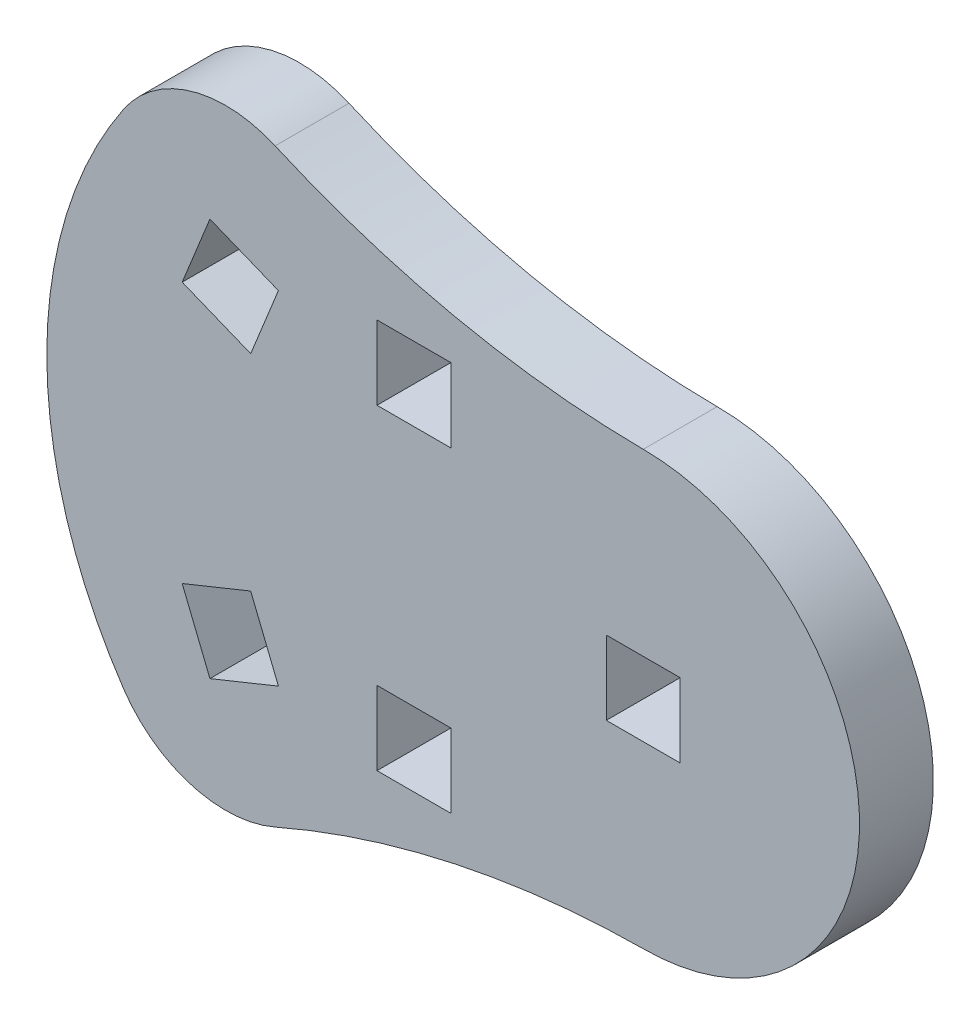
SolidWorks part; units mm, degrees
ref_plane "Front Plane" through (0, 0, 0) normal (0, 0, 1) x (1, 0, 0)
ref_plane "Top Plane" through (0, 0, 0) normal (0, 1, 0) x (1, 0, 0)
ref_plane "Right Plane" through (0, 0, 0) normal (1, 0, 0) x (0, 0, -1)
sketch "Sketch1" plane through (0, 0, 0) normal (0, 0, 1) x (1, 0, 0)
  line L0 (-6.7064, -5.985) -> (-6.7064, 4.461) construction
  line L1 (-1.524, -4.7878) -> (0, -4.7878)
  line L2 (-1.524, -4.7878) -> (-1.524, -3.2638)
  line L3 (-1.524, -3.2638) -> (0, -3.2638)
  line L4 (0, -4.7878) -> (0, -3.2638)
  line L5 (0, 1.7398) -> (-1.524, 1.7398)
  line L6 (0, 1.7398) -> (0, 3.2638)
  line L7 (0, 3.2638) -> (-1.524, 3.2638)
  line L8 (-1.524, 1.7398) -> (-1.524, 3.2638)
  line L9 (-6.7064, -5.223) -> (-6.7064, -6.747) construction
  line L10 (-6.7064, 5.223) -> (-6.7064, 3.699) construction
  line L12 (7.1074, 0) -> (0, 0) construction
  line L13 (3.9675, -1.524) -> (3.9675, 0) construction
  line L14 (-3.5039, -0.762) -> (1.0475, -0.762) construction
  line L15 (-3.5039, -1.524) -> (-3.5039, 0) construction
  line L16 (3.2055, -1.524) -> (4.7295, -1.524)
  line L17 (3.2055, -1.524) -> (3.2055, 0)
  line L18 (3.2055, 0) -> (4.7295, 0)
  line L19 (4.7295, -1.524) -> (4.7295, 0)
  line L20 (3.2055, -1.524) -> (4.7295, 0) construction
  line L21 (3.2055, 0) -> (4.7295, -1.524) construction
  line L22 (-5.5425, 1.9299) -> (-4.9707, 3.3425)
  line L23 (-4.1298, -2.882) -> (-5.5425, -3.4539)
  line L24 (-3.558, -4.2947) -> (-4.9707, -4.8665)
  line L25 (-4.1298, -2.882) -> (-3.558, -4.2947)
  line L26 (-5.5425, -3.4539) -> (-4.9707, -4.8665)
  line L27 (-4.1298, 1.358) -> (-3.558, 2.7707)
  line L28 (-3.558, 2.7707) -> (-4.9707, 3.3425)
  line L29 (-4.1298, 1.358) -> (-5.5425, 1.9299)
  arc A0 (-3.6258, -6.8461) -> (-6.7503, -5.9412) centre (-4.6453, -4.5197) cw
  arc A1 (-3.6258, 5.3221) -> (-6.7503, 4.4172) centre (-4.6453, 2.9957) ccw
  arc A2 (3.9675, -5.223) -> (3.9675, 3.699) centre (3.9675, -0.762) ccw
  arc A3 (3.9675, 3.699) -> (-3.6258, 5.3221) centre (4.1255, 23.011) cw
  arc A4 (3.9675, -5.223) -> (-3.6258, -6.8461) centre (4.1255, -24.535) ccw
  arc A5 (-6.7503, 4.4172) -> (-6.7503, -5.9412) centre (0.9191, -0.762) ccw
  point P18 (-6.7064, -0.762)
  point P49 (-5.2566, -7.6543)
  point P52 (-5.2566, 6.1303)
  dimension "D2" = 2.54
  dimension "D1" = 1.524
extrude "Boss-Extrude1" add sketch "Sketch1" against normal blind 1.524
